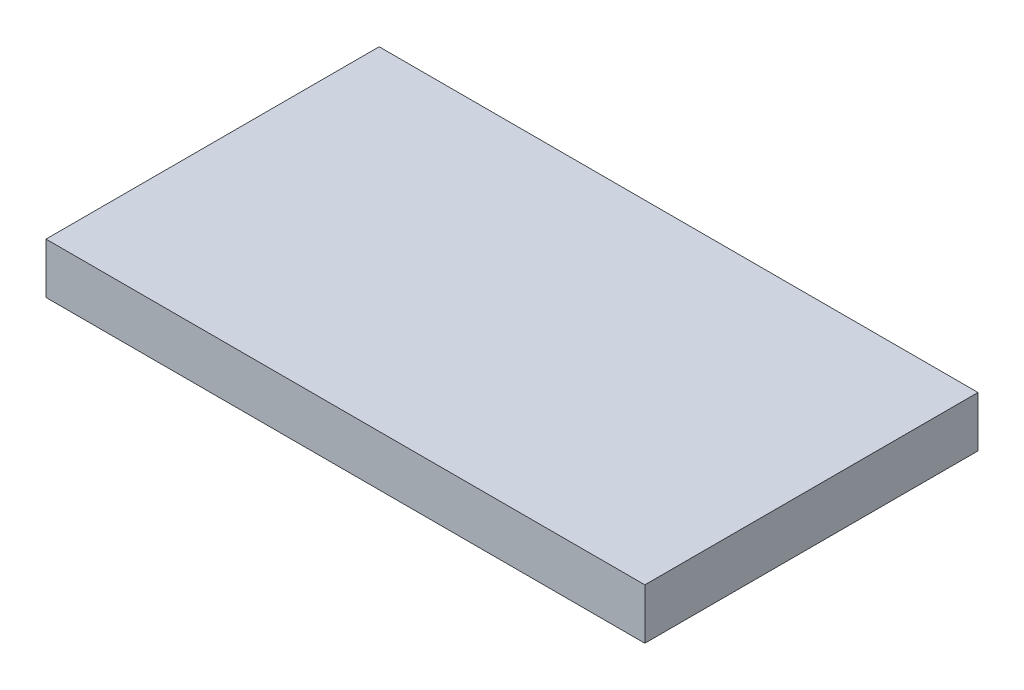
SolidWorks part; units mm, degrees
ref_plane "Front Plane" through (0, 0, 0) normal (0, 0, 1) x (1, 0, 0)
ref_plane "Top Plane" through (0, 0, 0) normal (0, 1, 0) x (1, 0, 0)
ref_plane "Right Plane" through (0, 0, 0) normal (1, 0, 0) x (0, 0, -1)
sketch "Sketch1" plane through (0, 0, 0) normal (0, 1, 0) x (1, 0, 0)
  line L1 (0, 0) -> (18.034, 0)
  line L2 (0, 0) -> (0, 10.033)
  line L3 (0, 10.033) -> (18.034, 10.033)
  line L4 (18.034, 0) -> (18.034, 10.033)
  dimension "D1" = 18.034
  dimension "D2" = 10.033
extrude "Boss-Extrude1" add sketch "Sketch1" along normal blind 1.524
